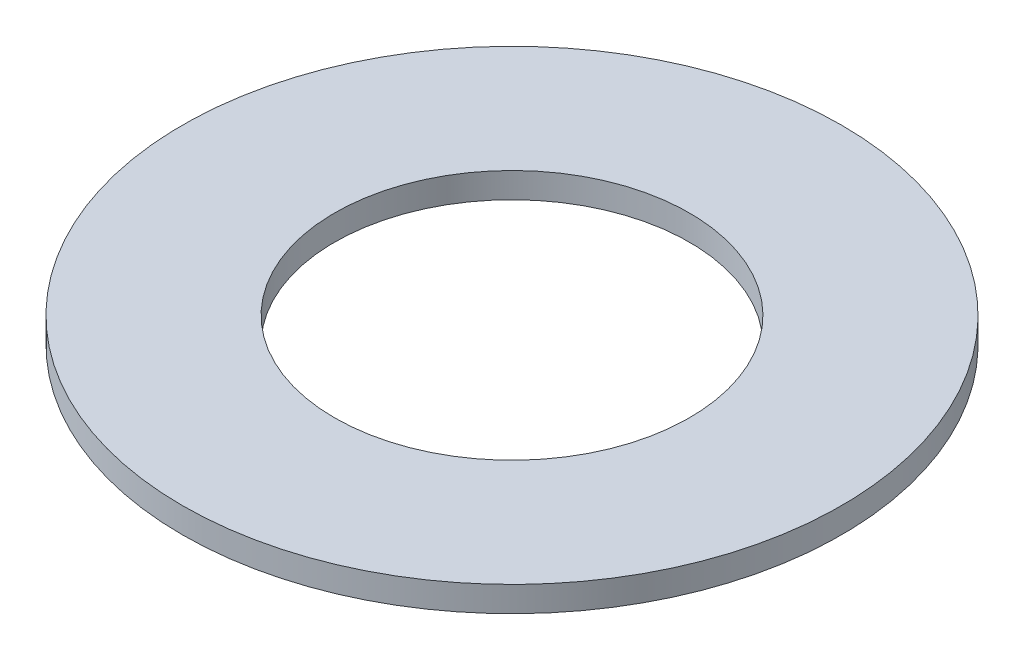
SolidWorks part; units mm, degrees
ref_plane "Front Plane" through (0, 0, 0) normal (0, 0, 1) x (1, 0, 0)
ref_plane "Top Plane" through (0, 0, 0) normal (0, 1, 0) x (1, 0, 0)
ref_plane "Right Plane" through (0, 0, 0) normal (1, 0, 0) x (0, 0, -1)
sketch "Sketch2" plane through (0, 0, 0) normal (0, 1, 0) x (1, 0, 0)
  circle A0 centre (0, 0) radius 70
  circle A1 centre (0, 0) radius 130
extrude "Boss-Extrude1" add sketch "Sketch2" along normal blind 10
